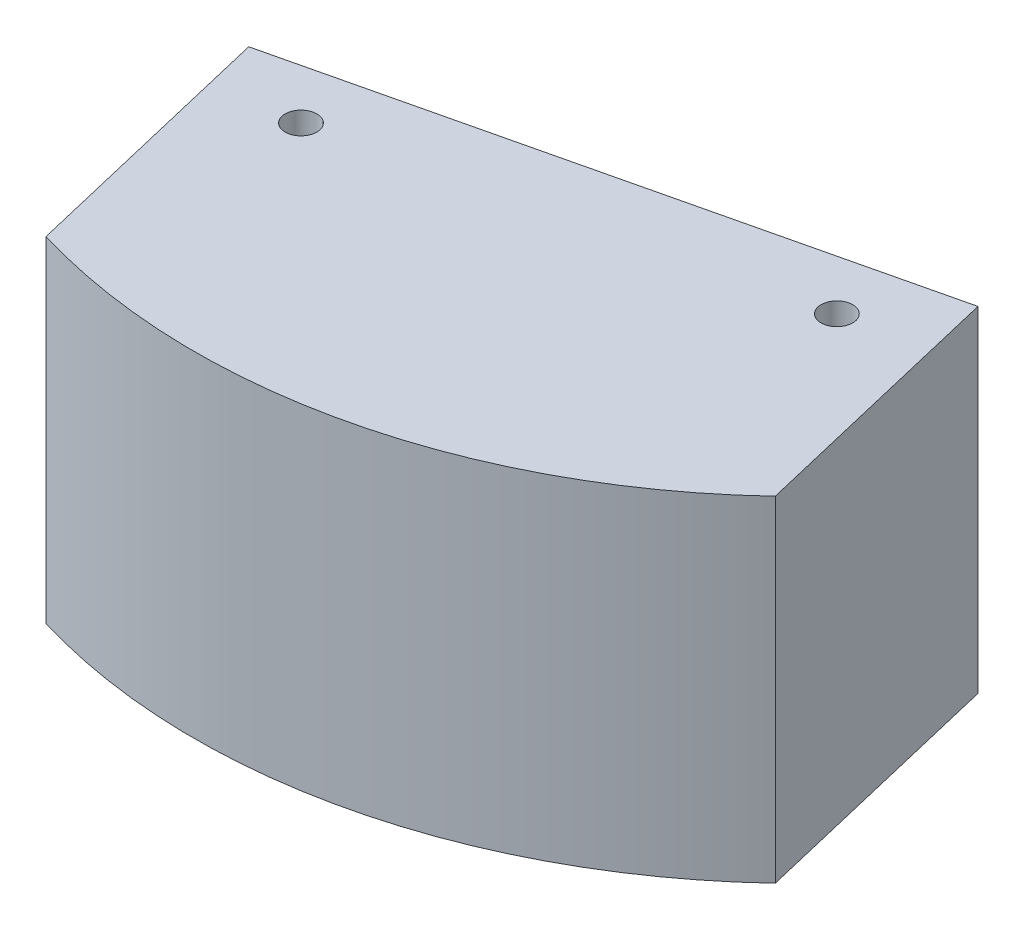
SolidWorks part; units mm, degrees
ref_plane "Front Plane" through (0, 0, 0) normal (0, 0, 1) x (1, 0, 0)
ref_plane "Top Plane" through (0, 0, 0) normal (0, 1, 0) x (1, 0, 0)
ref_plane "Right Plane" through (0, 0, 0) normal (1, 0, 0) x (0, 0, -1)
sketch "Sketch1" plane through (0, 0, 0) normal (0, 1, 0) x (1, 0, 0)
  line L3 (63.0178, -66.7821) -> (53.4682, -26.5063)
  line L5 (53.4682, -26.5063) -> (-35.8757, -47.6903)
  line L6 (-35.8757, -47.6903) -> (-26.3261, -87.9661)
  arc A0 (-26.3261, -87.9661) -> (63.0178, -66.7821) centre (0, 0) ccw
  dimension "D1" = 91.821
  dimension "D2" = 40.2758
  dimension "D3" = 40.2758
extrude "Boss-Extrude1" add sketch "Sketch1" along normal blind 50.8
sketch "Sketch2" plane through (0, 50.8, 0) normal (0, 1, 0) x (1, 0, 0)
  line L0 (-26.3261, -87.9661) -> (63.0178, -66.7821) construction
  line L1 (63.0178, -66.7821) -> (-35.8757, -47.6903) construction
  line L2 (-26.3261, -87.9661) -> (53.4682, -26.5063) construction
  line L3 (8.7963, -37.0983) -> (21.184, -89.3439) construction
  line L4 (53.4682, -26.5063) -> (-35.8757, -47.6903) construction
  arc A0 (-26.3261, -87.9661) -> (63.0178, -66.7821) centre (0, 0) ccw construction
  point P15 (0, 0)
  point P17 (23.9648, -101.0721)
sketch "Sketch5" plane through (0, 50.8, 0) normal (0, 1, 0) x (1, 0, 0)
  line L0 (45.8431, -47.0277) -> (57.6691, -44.2236) construction
  line L1 (63.0178, -66.7821) -> (53.4682, -26.5063) construction
  line L2 (57.6691, -44.2236) -> (45.8431, -47.0277) construction
  line L3 (45.8431, -47.0277) -> (41.6422, -29.3104) construction
  line L4 (53.4682, -26.5063) -> (-35.8757, -47.6903) construction
  line L5 (41.6422, -29.3104) -> (57.6691, -44.2236) construction
  line L6 (45.8431, -47.0277) -> (53.4682, -26.5063) construction
  line L7 (55.5686, -35.365) -> (-33.7753, -56.549) construction
  line L8 (-35.8757, -47.6903) -> (-26.3261, -87.9661) construction
  line L10 (-24.0126, -44.8775) -> (-21.9122, -53.7362) construction
hole_wizard "#12 (0.189) Diameter Hole1" positions "Sketch8" profile "Sketch9" hole size "#12" standard "ANSI Inch" end condition through all
sketch "Sketch8" plane through (0, 50.8, 0) normal (0, 1, 0) x (1, 0, 0)
  line L0 (45.8431, -47.0277) -> (41.6422, -29.3104) construction
  point P0 (-21.9122, -53.7362)
  point P3 (43.7426, -38.169)
sketch "Sketch9" plane through (-21.9122, 50.8, 53.7362) normal (1, 0, 0) x (0, 0, 1)
  line L0 (0, 0) -> (0, 50.8)
  line L1 (0, 50.8) -> (2.4003, 50.8)
  line L2 (2.4003, 50.8) -> (2.4003, 0)
  line L5 (2.4003, 0) -> (0, 0)
  line L11 (0, -6.35) -> (0, 107.95) construction
  dimension "Thru Hole Dia." = 4.8006
  dimension "Thru Hole Depth" = 50.8
